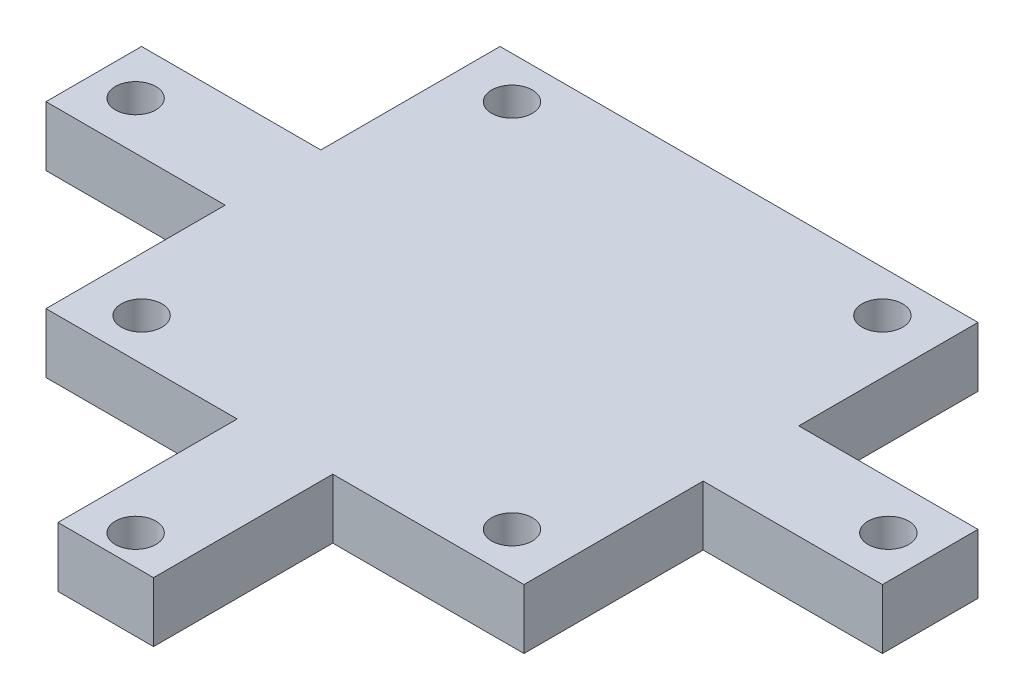
SolidWorks part; units mm, degrees
ref_plane "Alzado" through (0, 0, 0) normal (0, 0, 1) x (1, 0, 0)
ref_plane "Planta" through (0, 0, 0) normal (0, 1, 0) x (1, 0, 0)
ref_plane "Vista lateral" through (0, 0, 0) normal (1, 0, 0) x (0, 0, -1)
sketch "Croquis1" plane through (0, 0, 0) normal (0, 1, 0) x (1, 0, 0)
  line L0 (-35, 4) -> (-20, 4)
  line L1 (-15.5, 15.5) -> (15.5, 15.5) construction
  line L2 (-15.5, 15.5) -> (-15.5, -15.5) construction
  line L3 (-15.5, -15.5) -> (15.5, -15.5) construction
  line L4 (15.5, 15.5) -> (15.5, -15.5) construction
  line L5 (-15.5, 15.5) -> (15.5, -15.5) construction
  line L6 (-15.5, -15.5) -> (15.5, 15.5) construction
  line L7 (-20, 4) -> (-20, 19)
  line L8 (-20, 19) -> (20, 19)
  line L9 (20, 19) -> (20, 4)
  line L10 (20, 4) -> (35, 4)
  line L11 (0, 0) -> (8.6119, 0) construction
  line L12 (35, 4) -> (35, -4)
  line L13 (-35, 4) -> (-35, -4)
  line L14 (20, -4) -> (35, -4)
  line L15 (20, -19) -> (20, -4)
  line L16 (-20, -4) -> (-20, -19)
  line L17 (-35, -4) -> (-20, -4)
  line L18 (-20, -19) -> (-4, -19)
  line L19 (-4, -19) -> (-4, -34)
  line L20 (-4, -34) -> (4, -34)
  line L21 (4, -34) -> (4, -19)
  line L22 (4, -19) -> (20, -19)
  line L23 (0, 0) -> (0, 8.1765) construction
  circle A0 centre (-15.5, 15.5) radius 1.7
  circle A1 centre (15.5, 15.5) radius 1.7
  circle A2 centre (15.5, -15.5) radius 1.7
  circle A3 centre (-15.5, -15.5) radius 1.7
  circle A4 centre (0, 0) radius 25 construction
  circle A5 centre (0, 0) radius 31.5 construction
  circle A6 centre (-31.5, 0) radius 1.7
  circle A7 centre (0, -31.5) radius 1.7
  circle A8 centre (31.5, 0) radius 1.7
  point P0 (0, 0)
  point P16 (0, 0)
  point P27 (0, 0)
  point P31 (0, 19)
  point P36 (35, 0)
  point P41 (-35, 0)
  point P45 (0, -34)
  dimension "D2" = 3.4
  dimension "D4" = 50
  dimension "D6" = 3.4
  dimension "D1" = 31
  dimension "D8" = 15
  dimension "D9" = 15
  dimension "D10" = 40
  dimension "D11" = 8
  dimension "D12" = 8
  dimension "D5" = 6.5
  dimension "D3" = 4
  dimension "D7" = 3
extrude "Saliente-Extruir1" add sketch "Croquis1" along normal blind 5
